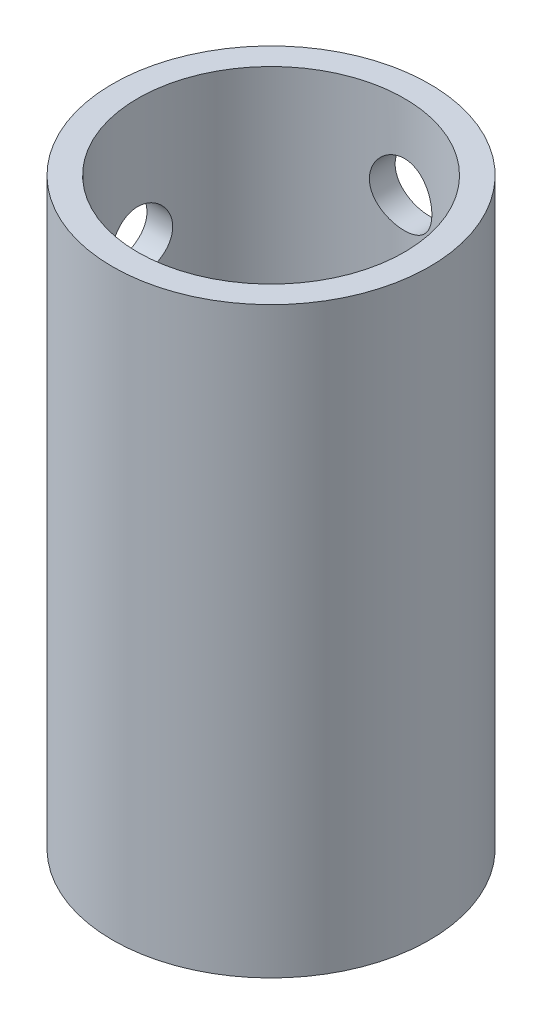
SolidWorks part; units mm, degrees
ref_plane "Front Plane" through (0, 0, 0) normal (0, 0, 1) x (1, 0, 0)
ref_plane "Top Plane" through (0, 0, 0) normal (0, 1, 0) x (1, 0, 0)
ref_plane "Right Plane" through (0, 0, 0) normal (1, 0, 0) x (0, 0, -1)
sketch "Sketch1" plane through (0, 0, 0) normal (0, 1, 0) x (1, 0, 0)
  circle A0 centre (0, 0) radius 24.1554
  circle A1 centre (0, 0) radius 20.32
  dimension "D1" = 48.3108
  dimension "D2" = 40.64
extrude "Boss-Extrude1" add sketch "Sketch1" along normal blind 88.9
sketch "Sketch2" plane through (0, 0, 0) normal (0, 0, 1) x (1, 0, 0)
  line L1 (20.32, 88.9) -> (-20.32, 88.9) construction
  line L2 (20.32, 88.9) -> (-20.32, 88.9) construction
  circle A0 centre (0, 76.2) radius 4.7625
  dimension "D1" = 9.525
  dimension "D2" = 12.7
extrude "Cut-Extrude1" cut sketch "Sketch2" against normal blind 33.5788
sketch "Sketch3" plane through (0, 0, 0) normal (1, 0, 0) x (0, 0, -1)
  line L0 (24.1554, 88.9) -> (-24.1554, 88.9) construction
  line L1 (24.1554, 88.9) -> (-24.1554, 88.9) construction
  circle A0 centre (0, 69.85) radius 4.7625
  dimension "D1" = 9.525
  dimension "D2" = 19.05
extrude "Cut-Extrude2" cut sketch "Sketch3" against normal blind 33.5788
